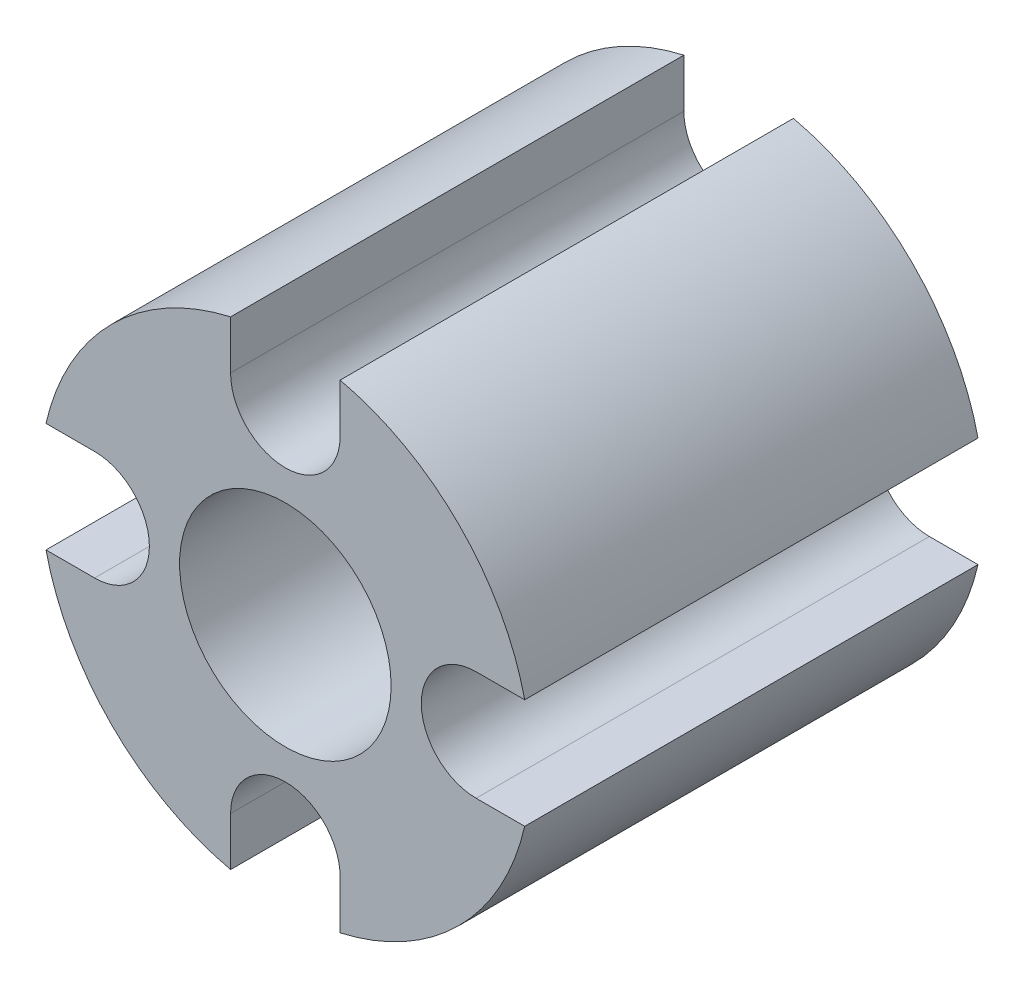
SolidWorks part; units mm, degrees
ref_plane "Plan de face" through (0, 0, 0) normal (0, 0, 1) x (1, 0, 0)
ref_plane "Plan de dessus" through (0, 0, 0) normal (0, 1, 0) x (1, 0, 0)
ref_plane "Plan de droite" through (0, 0, 0) normal (1, 0, 0) x (0, 0, -1)
sketch "Esquisse1" plane through (0, 0, 0) normal (0, 0, 1) x (1, 0, 0)
  line L0 (-0.725, 2.525) -> (-0.725, 3.1681)
  line L1 (0.725, 2.525) -> (0.725, 3.1681)
  line L2 (2.525, 0.725) -> (3.1681, 0.725)
  line L3 (2.525, -0.725) -> (3.1681, -0.725)
  line L4 (0.725, -2.525) -> (0.725, -3.1681)
  line L5 (-0.725, -2.525) -> (-0.725, -3.1681)
  line L6 (-2.525, -0.725) -> (-3.1681, -0.725)
  line L7 (-2.525, 0.725) -> (-3.1681, 0.725)
  arc A0 (-0.725, 3.1681) -> (-3.1681, 0.725) centre (0, 0) ccw
  circle A1 centre (0, 0) radius 1.4
  arc A2 (-0.725, 2.525) -> (0.725, 2.525) centre (0, 2.525) ccw
  arc A3 (2.525, 0.725) -> (2.525, -0.725) centre (2.525, 0) ccw
  arc A4 (0.725, -2.525) -> (-0.725, -2.525) centre (0, -2.525) ccw
  arc A5 (-2.525, -0.725) -> (-2.525, 0.725) centre (-2.525, 0) ccw
  arc A6 (-3.1681, -0.725) -> (-0.725, -3.1681) centre (0, 0) ccw
  arc A7 (0.725, -3.1681) -> (3.1681, -0.725) centre (0, 0) ccw
  arc A8 (3.1681, 0.725) -> (0.725, 3.1681) centre (0, 0) ccw
  point P26 (0, 0)
  dimension "D1" = 6.5
  dimension "D2" = 2.8
  dimension "D3" = 1.45
  dimension "D4" = 4
extrude "Boss.-Extru.2" add sketch "Esquisse1" along normal blind 6
